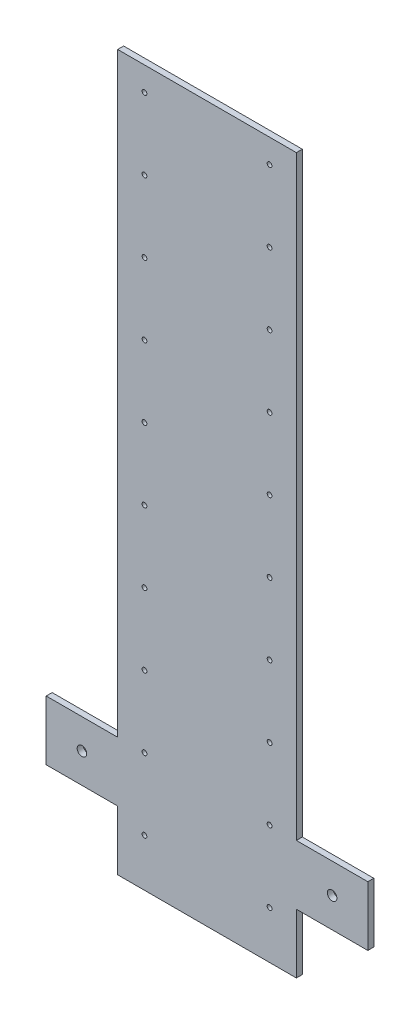
SolidWorks part; units mm, degrees
ref_plane "Front Plane" through (0, 0, 0) normal (0, 0, 1) x (1, 0, 0)
ref_plane "Top Plane" through (0, 0, 0) normal (0, 1, 0) x (1, 0, 0)
ref_plane "Right Plane" through (0, 0, 0) normal (1, 0, 0) x (0, 0, -1)
sketch "Sketch2" plane through (0, 0, 0) normal (0, 0, 1) x (1, 0, 0)
  line L0 (75, 300) -> (75, -200)
  line L1 (75, -200) -> (135, -200)
  line L2 (-75, 300) -> (-75, -200)
  line L3 (-75, -200) -> (-135, -200)
  line L4 (-135, -200) -> (-135, -250)
  line L5 (-135, -250) -> (-75, -250)
  line L6 (-75, -250) -> (-75, -300)
  line L7 (-75, -300) -> (75, -300)
  line L9 (75, 300) -> (-75, 300)
  line L10 (135, -200) -> (135, -250)
  line L11 (135, -250) -> (75, -250)
  line L12 (75, -250) -> (75, -300)
  circle A0 centre (-105, -225) radius 4
  circle A1 centre (105, -225) radius 4
  dimension "D1" = 500
  dimension "D7" = 8
  dimension "D2" = 50
  dimension "D3" = 30
  dimension "D4" = 60
  dimension "D5" = 50
  dimension "D6" = 150
extrude "Boss-Extrude1" add sketch "Sketch2" along normal blind 5
sketch "Sketch3" plane through (0, 0, 5) normal (0, 0, 1) x (1, 0, 0)
  circle A0 centre (-52.5, 280) radius 2
  circle A1 centre (-52.5, 220) radius 2
  circle A2 centre (-52.5, 160) radius 2
  circle A3 centre (-52.5, 100) radius 2
  circle A4 centre (-52.5, 40) radius 2
  circle A5 centre (-52.5, -20) radius 2
  circle A6 centre (-52.5, -80) radius 2
  circle A7 centre (-52.5, -140) radius 2
  circle A8 centre (-52.5, -200) radius 2
  circle A9 centre (-52.5, -260) radius 2
  circle A10 centre (52.5, -260) radius 2
  circle A11 centre (52.5, -200) radius 2
  circle A12 centre (52.5, -140) radius 2
  circle A13 centre (52.5, -80) radius 2
  circle A14 centre (52.5, -20) radius 2
  circle A15 centre (52.5, 40) radius 2
  circle A16 centre (52.5, 100) radius 2
  circle A17 centre (52.5, 160) radius 2
  circle A18 centre (52.5, 220) radius 2
  circle A19 centre (52.5, 280) radius 2
extrude "Cut-Extrude1" cut sketch "Sketch3" against normal blind 5
